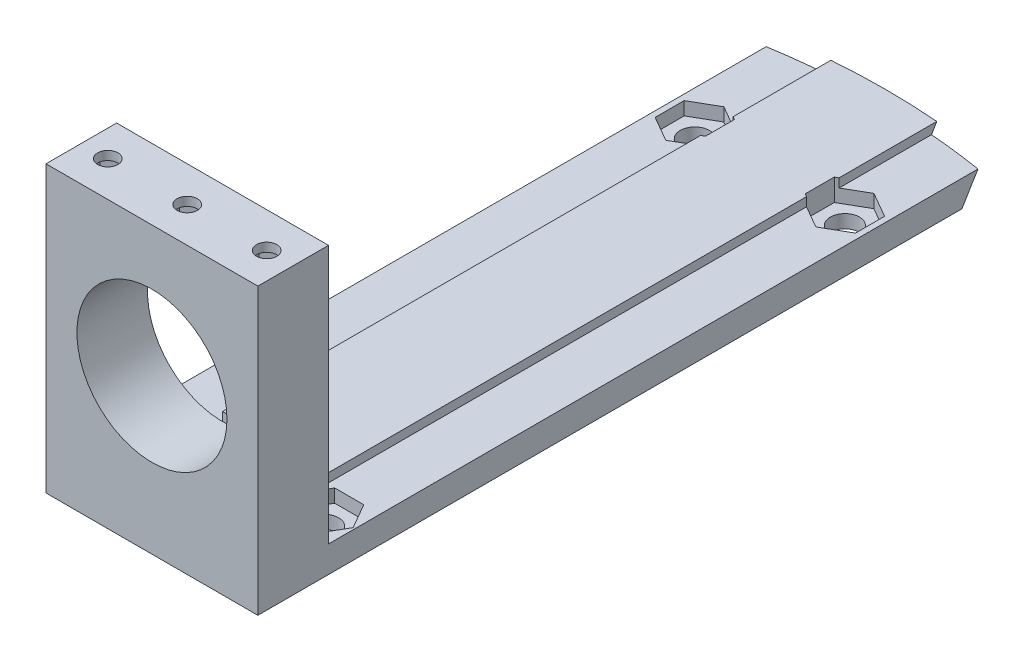
SolidWorks part; units mm, degrees
ref_plane "Front Plane" through (0, 0, 0) normal (0, 0, 1) x (1, 0, 0)
ref_plane "Top Plane" through (0, 0, 0) normal (0, 1, 0) x (1, 0, 0)
ref_plane "Right Plane" through (0, 0, 0) normal (1, 0, 0) x (0, 0, -1)
sketch "Sketch1" plane through (0, 0, 0) normal (0, 1, 0) x (1, 0, 0)
  line L1 (0, 0) -> (24, 0)
  line L2 (0, 0) -> (0, 81.5022)
  line L3 (0, 81.5022) -> (24, 81.5022)
  line L4 (24, 0) -> (24, 81.5022)
  dimension "D1" = 24
extrude "Boss-Extrude1" add sketch "Sketch1" along normal blind 3
sketch "Sketch2" plane through (0, 0, 0) normal (0, 1, 0) x (1, 0, 0)
  line L0 (0, 0) -> (24, 0) construction
  circle A0 centre (3.5, 3) radius 1.65
  circle A1 centre (12, 3) radius 1.65
  circle A2 centre (20.5, 3) radius 1.65
  circle A6 centre (3.5, 62) radius 1.65
  circle A8 centre (20.5, 62) radius 1.65
  circle A9 centre (12, 32.5) radius 1.65
  circle A10 centre (3.5, 32.5) radius 1.65
  circle A11 centre (20.5, 32.5) radius 1.65
  circle A12 centre (12, 62) radius 1.65
  point P9 (12, 0)
  dimension "D1" = 3.3
  dimension "D2" = 3
  dimension "D3" = 8.5
  dimension "D4" = 8.5
  dimension "D5" = 3
  dimension "D6" = 59
extrude "Cut-Extrude1" cut sketch "Sketch2" along normal through all
sketch "Sketch3" plane through (0, 0, 0) normal (0, 0, 1) x (1, 0, 0)
  line L0 (0, 3) -> (24, 3) construction
  line L1 (6, 3) -> (18, 3)
  line L2 (6, 3) -> (6, 4)
  line L3 (6, 4) -> (18, 4)
  line L4 (18, 3) -> (18, 4)
  line L5 (77.5014, 4) -> (-53.5014, 4) construction
  point P11 (12, 3)
  dimension "D1" = 12
  dimension "D2" = 12
extrude "Boss-Extrude2" add sketch "Sketch3" against normal up to surface (75.5022 mm away) from offset 6 up to face at (12, 1.5, -81.5022) offset against normal yes
ref_plane "Plane1" through (12, 0, 0) normal (-1, 0, 0) x (0, 0, 1)
sketch "Sketch4" plane through (12, 0, 0) normal (1, 0, 0) x (0, 0, -1)
  line L0 (94.4965, 36.2415) -> (19.4137, -88.8964)
  line L1 (19.4137, -88.8964) -> (139.5903, -88.8964)
  line L2 (139.5903, -88.8964) -> (139.5903, 36.2415)
  line L3 (139.5903, 36.2415) -> (94.4965, 36.2415)
  line L4 (73, -6) -> (79, 4) construction
  line L6 (0, 0) -> (0, 3) construction
  dimension "D1" = 3.3
revolve "Cut-Revolve1" cut sketch "Sketch4" angle 360 about L6
sketch "Sketch5" plane through (0, 3, 0) normal (0, 1, 0) x (1, 0, 0)
  line L0 (18, 74.3097) -> (18, 6) construction
  line L1 (15.2909, 3) -> (13.6454, 5.85)
  line L2 (13.6454, 5.85) -> (10.3546, 5.85)
  line L3 (10.3546, 5.85) -> (8.7091, 3)
  line L4 (8.7091, 3) -> (10.3546, 0.15)
  line L5 (10.3546, 0.15) -> (13.6454, 0.15)
  line L6 (13.6454, 0.15) -> (15.2909, 3)
  line L7 (23.7909, 3) -> (22.1454, 5.85)
  line L8 (22.1454, 5.85) -> (18.8546, 5.85)
  line L9 (18.8546, 5.85) -> (17.2091, 3)
  line L10 (17.2091, 3) -> (18.8546, 0.15)
  line L11 (18.8546, 0.15) -> (22.1454, 0.15)
  line L12 (22.1454, 0.15) -> (23.7909, 3)
  line L13 (6.7909, 3) -> (5.1454, 5.85)
  line L14 (5.1454, 5.85) -> (1.8546, 5.85)
  line L15 (1.8546, 5.85) -> (0.2091, 3)
  line L16 (0.2091, 3) -> (1.8546, 0.15)
  line L17 (1.8546, 0.15) -> (5.1454, 0.15)
  line L18 (5.1454, 0.15) -> (6.7909, 3)
  line L31 (6.35, 63.6454) -> (3.5, 65.2909)
  line L32 (3.5, 65.2909) -> (0.65, 63.6454)
  line L33 (0.65, 63.6454) -> (0.65, 60.3546)
  line L34 (0.65, 60.3546) -> (3.5, 58.7091)
  line L35 (3.5, 58.7091) -> (6.35, 60.3546)
  line L36 (6.35, 60.3546) -> (6.35, 63.6454)
  line L37 (23.35, 63.6454) -> (20.5, 65.2909)
  line L38 (20.5, 65.2909) -> (17.65, 63.6454)
  line L39 (17.65, 63.6454) -> (17.65, 60.3546)
  line L40 (17.65, 60.3546) -> (20.5, 58.7091)
  line L41 (20.5, 58.7091) -> (23.35, 60.3546)
  line L42 (23.35, 60.3546) -> (23.35, 63.6454)
  line L43 (6, 74.3097) -> (6, 6) construction
  circle A0 centre (12, 3) radius 2.85 construction
  circle A1 centre (20.5, 3) radius 2.85 construction
  circle A2 centre (3.5, 3) radius 2.85 construction
  circle A3 centre (3.5, 62) radius 2.85 construction
  circle A4 centre (20.5, 62) radius 2.85 construction
  dimension "D1" = 5.7
  dimension "D2" = 5.7
extrude "Cut-Extrude2" cut sketch "Sketch5" against normal blind 1.5 and the other way through all
sketch "Sketch6" plane through (0, 0, 0) normal (0, 0, 1) x (1, 0, 0)
  line L0 (12, 2.2) -> (12, -2.2) construction
  line L1 (0, 0) -> (24, 0)
  line L2 (0, 0) -> (0, 32.3)
  line L3 (0, 32.3) -> (24, 32.3)
  line L4 (24, 0) -> (24, 32.3)
  circle A0 centre (12, 17.5) radius 8.5
  dimension "D2" = 17
  dimension "D1" = 32.3
  dimension "D3" = 17.5
extrude "Boss-Extrude3" add sketch "Sketch6" along normal blind 8
sketch "Sketch9" plane through (0, 32.3, 0) normal (0, 1, 0) x (1, 0, 0)
  line L0 (0, -4) -> (6, -4) construction
  line L1 (0, -8) -> (0, 0) construction
  line L2 (6, -4) -> (9, -4) construction
  line L3 (9, -4) -> (15, -4) construction
  line L4 (15, -4) -> (18, -4) construction
  line L5 (18, -4) -> (24, -4) construction
  line L6 (24, -8) -> (24, 0) construction
  circle A0 centre (3, -4) radius 1.15
  circle A1 centre (12, -4) radius 1.15
  circle A2 centre (21, -4) radius 1.15
  dimension "D1" = 2.3
  dimension "D2" = 6
extrude "Cut-Extrude3" cut sketch "Sketch9" against normal blind 5
sketch "Sketch10" plane through (0, 32.3, 0) normal (0, 1, 0) x (1, 0, 0)
  line L1 (3, -6.4249) -> (5.1, -5.2124)
  line L2 (5.1, -5.2124) -> (5.1, -2.7876)
  line L3 (5.1, -2.7876) -> (3, -1.5751)
  line L4 (3, -1.5751) -> (0.9, -2.7876)
  line L5 (0.9, -2.7876) -> (0.9, -5.2124)
  line L6 (0.9, -5.2124) -> (3, -6.4249)
  line L7 (12, -6.4249) -> (14.1, -5.2124)
  line L8 (14.1, -5.2124) -> (14.1, -2.7876)
  line L9 (14.1, -2.7876) -> (12, -1.5751)
  line L10 (12, -1.5751) -> (9.9, -2.7876)
  line L11 (9.9, -2.7876) -> (9.9, -5.2124)
  line L12 (9.9, -5.2124) -> (12, -6.4249)
  line L13 (21, -6.4249) -> (23.1, -5.2124)
  line L14 (23.1, -5.2124) -> (23.1, -2.7876)
  line L15 (23.1, -2.7876) -> (21, -1.5751)
  line L16 (21, -1.5751) -> (18.9, -2.7876)
  line L17 (18.9, -2.7876) -> (18.9, -5.2124)
  line L18 (18.9, -5.2124) -> (21, -6.4249)
  circle A0 centre (3, -4) radius 2.1 construction
  circle A1 centre (12, -4) radius 2.1 construction
  circle A2 centre (21, -4) radius 2.1 construction
  dimension "D1" = 4.2
extrude "Cut-Extrude4" cut sketch "Sketch10" against normal blind 1.8 from offset 1
